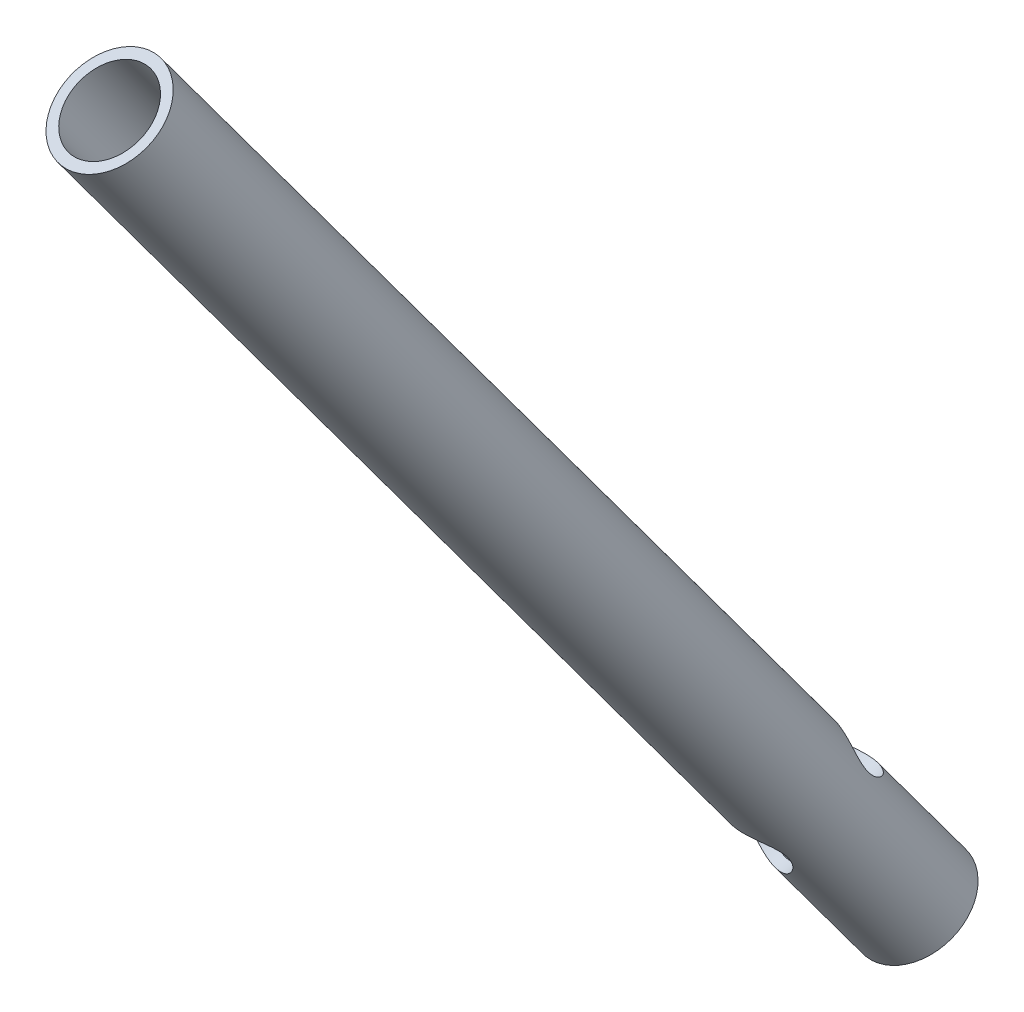
SolidWorks part; units mm, degrees
ref_plane "Front Plane" through (0, 0, 0) normal (0, 0, 1) x (1, 0, 0)
ref_plane "Top Plane" through (0, 0, 0) normal (0, 1, 0) x (1, 0, 0)
ref_plane "Right Plane" through (0, 0, 0) normal (1, 0, 0) x (0, 0, -1)
sketch "Sketch1" plane through (-18.2636, 106.3523, 73.9598) normal (-0.1396, 0.813, 0.5653) x (0.9897, 0.1321, 0.0544)
  circle A0 centre (75.6641, -74.9887) radius 5
  circle A1 centre (75.6641, -74.9887) radius 4
  dimension "D1" = 8
  dimension "D2" = 10
extrude "Boss-Extrude1" add sketch "Sketch1" along normal blind 80 and the other way blind 30
sketch "Sketch2" plane through (167.4612, -27.8298, 89.2991) normal (-0.176, -0.5822, 0.7938) x (0.9744, 0.0113, 0.2243)
  circle A0 centre (-93.2969, 111.3401) radius 3
  dimension "D1" = 6
extrude "Cut-Extrude1" cut sketch "Sketch2" against normal through all both and the other way through all
